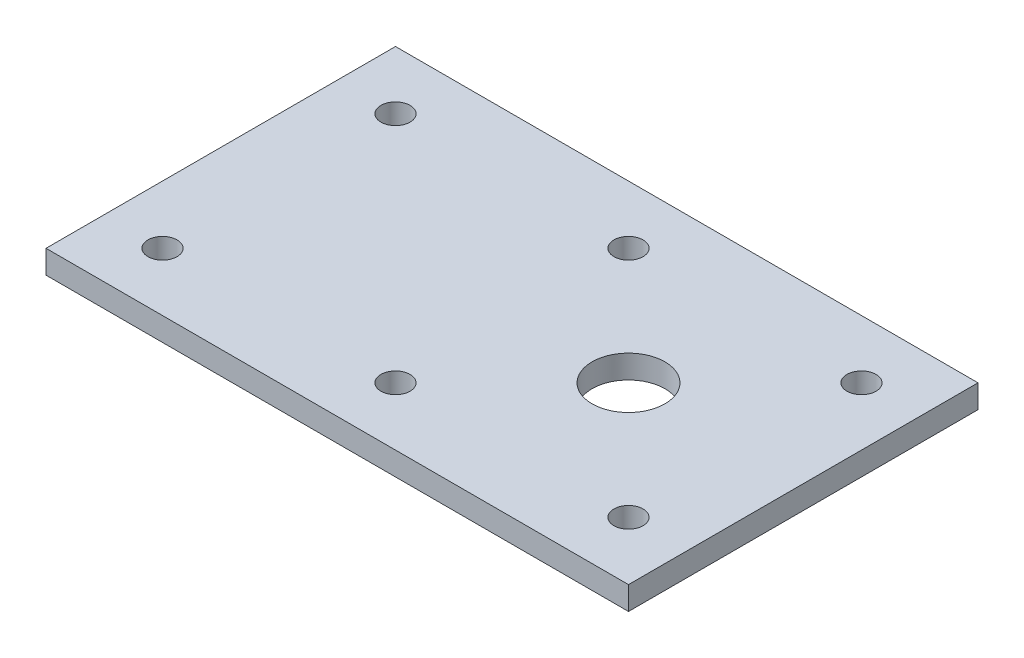
SolidWorks part; units mm, degrees
ref_plane "Front Plane" through (0, 0, 0) normal (0, 0, 1) x (1, 0, 0)
ref_plane "Top Plane" through (0, 0, 0) normal (0, 1, 0) x (1, 0, 0)
ref_plane "Right Plane" through (0, 0, 0) normal (1, 0, 0) x (0, 0, -1)
sketch "Sketch2" plane through (0, 0, 0) normal (0, 1, 0) x (1, 0, 0)
  line L0 (109.6408, -20.1134) -> (-90.3592, -20.1134) construction
  line L1 (-90.3592, 39.8866) -> (109.6408, 39.8866)
  line L2 (-90.3592, 39.8866) -> (-90.3592, -80.1134)
  line L3 (-90.3592, -80.1134) -> (109.6408, -80.1134)
  line L4 (109.6408, 39.8866) -> (109.6408, -80.1134)
  line L5 (-90.3592, -20.1134) -> (9.0737, -20.1134) construction
  line L8 (10.586, -20.983) -> (8.6957, -19.8488) construction
  line L9 (8.6957, -19.8488) -> (9.0737, -19.8488) construction
  line L10 (9.0737, -19.8488) -> (9.4518, -20.2268) construction
  dimension "D1" = 200
  dimension "D2" = 120
extrude "Boss-Extrude1" add sketch "Sketch2" along normal blind 8 contours L3 L4 L1 L2
sketch "Sketch4" plane through (0, 8, 0) normal (0, 1, 0) x (1, 0, 0)
  line L1 (-90.3592, 39.8866) -> (109.6408, 39.8866) construction
  line L2 (-90.3592, 39.8866) -> (-90.3592, -80.1134) construction
  circle A1 centre (-70.3592, 19.8866) radius 5
  dimension "D1" = 10
  dimension "D2" = 20
  dimension "D3" = 20
extrude "Cut-Extrude1" cut sketch "Sketch4" against normal blind 8
pattern_linear "LPattern2" count 2 spacing 80 along (0, 0, 1) count 3 spacing 80 along (1, 0, 0) of "Cut-Extrude1"
sketch "Sketch5" plane through (0, 0, 0) normal (0, -1, 0) x (1, 0, 0)
  line L2 (-90.3592, -39.8866) -> (109.6408, -39.8866) construction
  line L3 (109.6408, -39.8866) -> (109.6408, 80.1134) construction
  circle A0 centre (49.6408, 20.1134) radius 12.5
  point P2 (0, 0)
  point P3 (0, 0)
  point P4 (48.7401, 16.0408)
  dimension "D1" = 25
  dimension "D2" = 60
  dimension "D3" = 60
extrude "Cut-Extrude2" cut sketch "Sketch5" against normal blind 50
